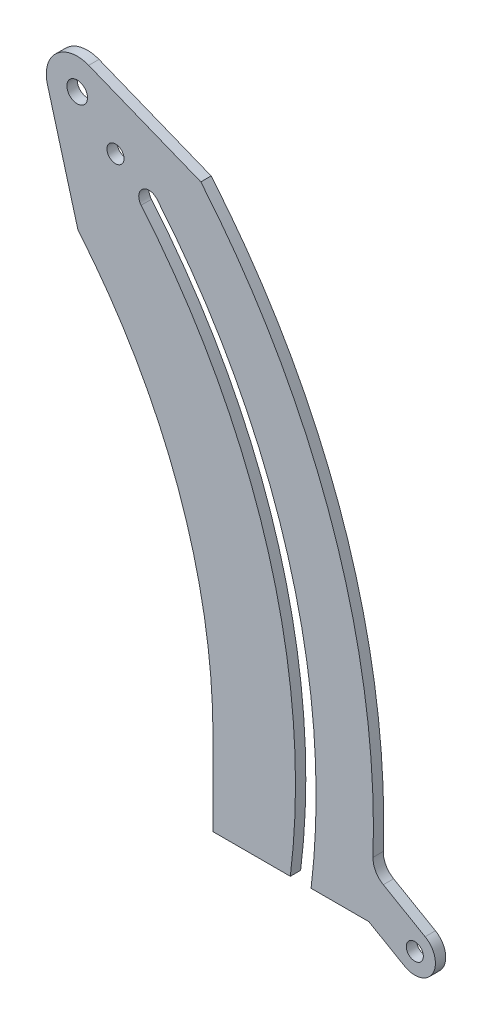
SolidWorks part; units mm, degrees
material "6061-T6 (SS)"
ref_plane "Front Plane" through (0, 0, 0) normal (0, 0, 1) x (1, 0, 0)
ref_plane "Top Plane" through (0, 0, 0) normal (0, 1, 0) x (1, 0, 0)
ref_plane "Right Plane" through (0, 0, 0) normal (1, 0, 0) x (0, 0, -1)
sketch "Sketch2" plane through (0, 0, 0) normal (0, 0, 1) x (1, 0, 0)
  line L12 (155.6602, 130.6144) -> (160.5246, 134.6961)
  line L13 (208.0049, -25.4) -> (225.7757, -25.4)
  line L14 (174.0453, 146.0413) -> (139.5033, 159.8514)
  line L15 (126.7844, 148.4774) -> (136.2027, 114.2876)
  line L16 (177.8, 0) -> (177.8, -25.4)
  line L17 (177.8, -25.4) -> (201.6062, -25.4)
  arc A10 (201.6062, -25.4) -> (155.6602, 130.6144) centre (0, 0) ccw
  arc A11 (208.0049, -25.4) -> (160.5246, 134.6961) centre (0, 0) ccw
  arc A12 (225.7757, -25.4) -> (174.0453, 146.0413) centre (0, 0) ccw
  arc A13 (139.5033, 159.8514) -> (126.7844, 148.4774) centre (135.9673, 151.007) ccw
  arc A14 (177.8, 0) -> (136.2027, 114.2876) centre (0, 0) ccw
extrude "Copied sketch - dont mess with" add sketch "Sketch2" along normal blind 3.175
sketch "Sketch3" plane through (0, 0, 3.175) normal (0, 0, 1) x (1, 0, 0)
  circle A0 centre (135.9673, 151.007) radius 3.175
  dimension "D1" = 6.35
extrude "Hole for top support bracing" cut sketch "Sketch3" against normal through all
sketch "Sketch4" plane through (0, 0, 3.175) normal (0, 0, 1) x (1, 0, 0)
  line L0 (155.6602, 130.6144) -> (160.5246, 134.6961) construction
  circle A0 centre (158.0924, 132.6553) radius 3.175
extrude "Making it machinable" cut sketch "Sketch4" against normal through all
sketch "Sketch5" plane through (0, 0, 3.175) normal (0, 0, 1) x (1, 0, 0)
  line L0 (225.7757, -25.4) -> (236.7743, -31.75)
  line L1 (226.9142, -11.3926) -> (243.1243, -20.7515)
  line L2 (208.0049, -25.4) -> (225.7757, -25.4) construction
  arc A0 (225.7757, -25.4) -> (174.0453, 146.0413) centre (0, 0) ccw construction
  arc A1 (225.7757, -25.4) -> (226.9142, -11.3926) centre (0, 0) ccw
  arc A2 (236.7743, -31.75) -> (243.1243, -20.7515) centre (239.9493, -26.2507) ccw
  circle A3 centre (239.9493, -26.2507) radius 2.6289
  dimension "D1" = 6.35
  dimension "D3" = 5.2578
  dimension "D2" = 150
  dimension "D4" = 12.7
extrude "Thing for hardstop" add sketch "Sketch5" against normal blind 3.175
fillet "Fillet1" radius 6.35 1 edges at (226.9142, -11.3926, 1.5875)
sketch "Sketch6" plane through (0, 0, 3.175) normal (0, 0, 1) x (1, 0, 0)
  line L0 (135.9673, 151.007) -> (147.7648, 140.3846) construction
  line L1 (0, 0) -> (135.9673, 151.007) construction
  circle A0 centre (147.7648, 140.3846) radius 2.6289
  dimension "D1" = 5.2578
  dimension "D2" = 15.875
extrude "Cut-Extrude1" cut sketch "Sketch6" against normal through all
